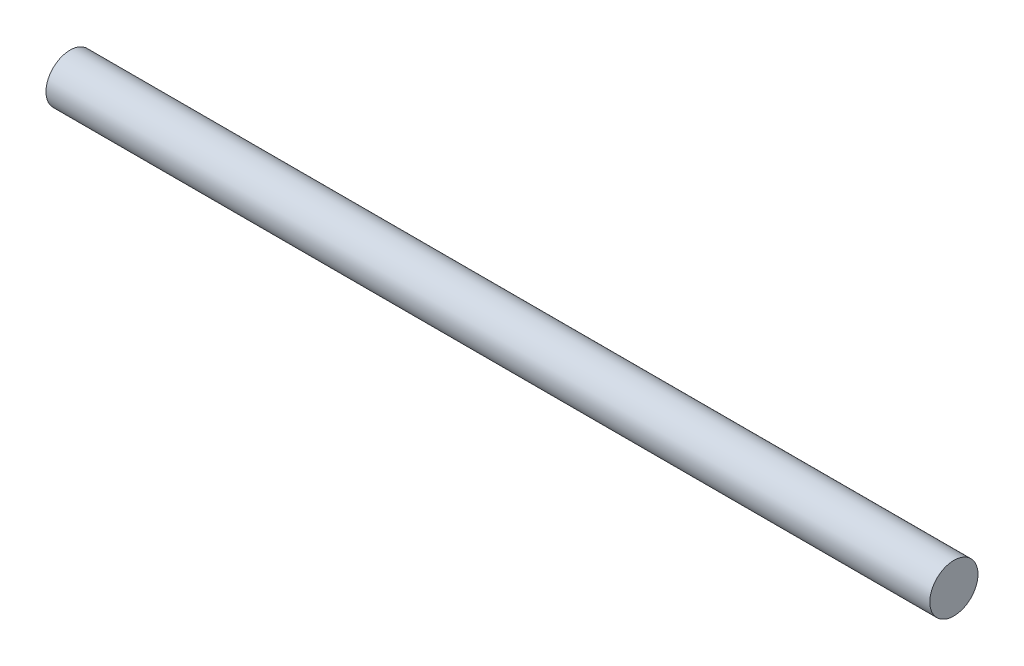
SolidWorks part; units mm, degrees
material "Plain Carbon Steel"
ref_plane "Front Plane" through (0, 0, 0) normal (0, 0, 1) x (1, 0, 0)
ref_plane "Top Plane" through (0, 0, 0) normal (0, 1, 0) x (1, 0, 0)
ref_plane "Right Plane" through (0, 0, 0) normal (1, 0, 0) x (0, 0, -1)
sketch "Sketch1" plane through (0, 0, 0) normal (1, 0, 0) x (0, 0, -1)
  circle A0 centre (0, 0) radius 1.5
  dimension "D1" = 3
extrude "Boss-Extrude1" add sketch "Sketch1" along normal mid plane 55
